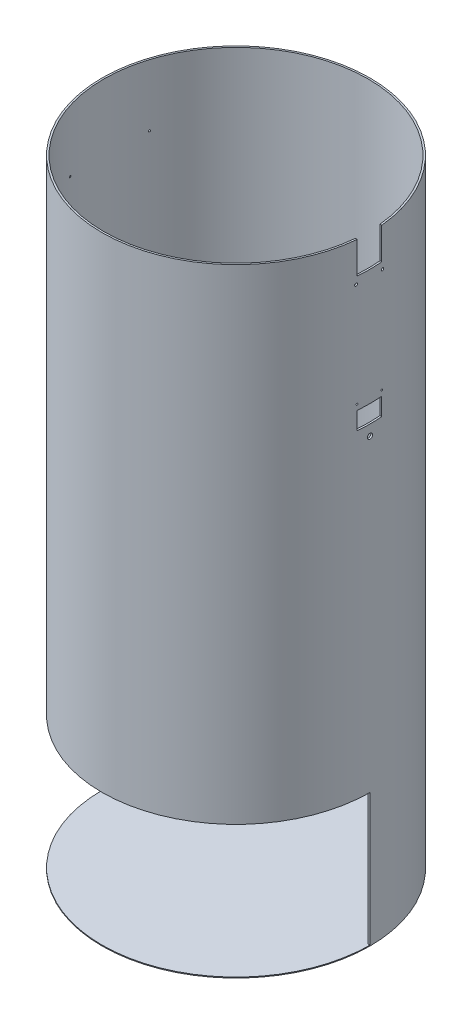
SolidWorks part; units mm, degrees
ref_plane "Plan de face" through (0, 0, 0) normal (0, 0, 1) x (1, 0, 0)
ref_plane "Plan de dessus" through (0, 0, 0) normal (0, 1, 0) x (1, 0, 0)
ref_plane "Plan de droite" through (0, 0, 0) normal (1, 0, 0) x (0, 0, -1)
sketch "Esquisse1" plane through (0, 0, 0) normal (0, 1, 0) x (1, 0, 0)
  circle A0 centre (0, 0) radius 150
  circle A1 centre (0, 0) radius 152
  dimension "D1" = 300
  dimension "D2" = 304
extrude "Boss.-Extru.1" add sketch "Esquisse1" against normal blind 700
sketch "Esquisse2" plane through (0, -700, 0) normal (0, -1, 0) x (-1, 0, 0)
  circle A0 centre (0, 0) radius 152
extrude "Boss.-Extru.2" add sketch "Esquisse2" along normal blind 1
sketch "Esquisse6" plane through (0, 0, 0) normal (0, 0, 1) x (1, 0, 0)
  line L0 (-152, 0) -> (-152, -701) construction
  line L1 (-152, -550) -> (152, -550)
  line L2 (-152, -550) -> (-152, -700)
  line L3 (-152, -700) -> (152, -700)
  line L4 (152, -550) -> (152, -700)
  line L5 (152, -701) -> (152, 0) construction
  line L6 (-152, -701) -> (152, -701) construction
  dimension "D1" = 1
  dimension "D2" = 150
extrude "Enlèv. mat.-Extru.3" cut sketch "Esquisse6" along normal blind 152
sketch "Esquisse7" plane through (0, 0, 0) normal (1, 0, 0) x (0, 0, -1)
  line L0 (150, 0) -> (-150, 0) construction
  line L1 (-14, 0) -> (-4, 0)
  line L2 (-14, 0) -> (-14, -36)
  line L4 (14, 0) -> (14, -36)
  line L5 (0, -701) -> (0, 0) construction
  line L6 (-14, -36) -> (14, -36)
  line L7 (4, 0) -> (14, 0)
  circle A0 centre (0, 0) radius 4
  circle A3 centre (-15, -44) radius 1.5
  circle A4 centre (15, -44) radius 1.5
  dimension "D1" = 8
  dimension "D5" = 3
  dimension "D6" = 3
  dimension "D2" = 44
  dimension "D3" = 44
  dimension "D4" = 14
  dimension "D7" = 36
  dimension "D8" = 15
  dimension "D9" = 15
extrude "Enlèv. mat.-Extru.4" cut sketch "Esquisse7" along normal blind 240 contours A3 | A4 | A0 L1 L2 L6 L4 L7
sketch "Esquisse8" plane through (0, 0, 0) normal (1, 0, 0) x (0, 0, -1)
  line L0 (-126.5804, -200) -> (177.4196, -200) construction
  line L5 (-18.1083, -162) -> (66.7697, -162) construction
  line L6 (0, -159.5957) -> (0, -167.0076) construction
  line L8 (-14, -168) -> (14, -168)
  line L9 (0, -701) -> (0, -36) construction
  line L10 (-14, -168) -> (-14, -188)
  line L11 (-14, -188) -> (14, -188)
  line L12 (14, -168) -> (14, -188)
  circle A0 centre (0, -200) radius 3
  circle A3 centre (-14, -162) radius 1
  circle A4 centre (14, -162) radius 1
  dimension "D1" = 6
  dimension "D3" = 20
  dimension "D7" = 2
  dimension "D8" = 2
  dimension "D2" = 6
  dimension "D9" = 38
  dimension "D10" = 14
  dimension "D11" = 14
extrude "Enlèv. mat.-Extru.5" cut sketch "Esquisse8" along normal blind 220
sketch "Esquisse9" plane through (0, 0, 0) normal (1, 0, 0) x (0, 0, -1)
  circle A0 centre (0, -200) radius 1
  dimension "D1" = 2
extrude "Enlèv. mat.-Extru.6" cut sketch "Esquisse9" against normal blind 170
sketch "Esquisse10" plane through (0, 0, 0) normal (1, 0, 0) x (0, 0, -1)
  line L0 (0, -20) -> (0, -120) construction
  line L1 (-75, -120) -> (75, -120)
  line L2 (-75, -120) -> (-75, -20)
  line L3 (-75, -20) -> (75, -20)
  line L4 (75, -120) -> (75, -20)
  line L5 (-75, -120) -> (75, -20) construction
  line L6 (-75, -20) -> (75, -120) construction
  line L7 (150, 0) -> (-150, 0) construction
  circle A0 centre (-45, -70) radius 1
  circle A2 centre (45, -70) radius 1
  point P0 (0, -70)
  point P14 (0, 0)
  point P15 (0, 0)
  dimension "D2" = 2
  dimension "D3" = 30
  dimension "D1" = 150
  dimension "D4" = 100
  dimension "D5" = 20
extrude "Enlèv. mat.-Extru.8" cut sketch "Esquisse10" against normal blind 220 contours A0 | A2
